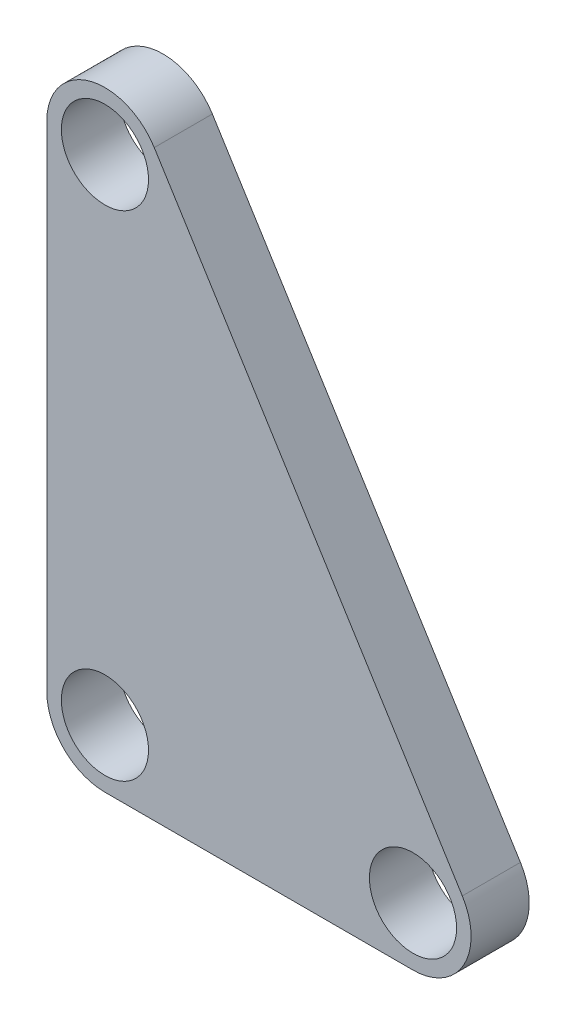
SolidWorks part; units mm, degrees
ref_plane "Front Plane" through (0, 0, 0) normal (0, 0, 1) x (1, 0, 0)
ref_plane "Top Plane" through (0, 0, 0) normal (0, 1, 0) x (1, 0, 0)
ref_plane "Right Plane" through (0, 0, 0) normal (1, 0, 0) x (0, 0, -1)
sketch "Sketch1" plane through (0, 0, 0) normal (0, 0, 1) x (1, 0, 0)
  line L0 (0, 9.5) -> (0, 1)
  line L1 (1, 0) -> (6.3, 0)
  line L2 (7.1486, 1.5291) -> (1.8486, 10.0291)
  arc A0 (1.8486, 10.0291) -> (0, 9.5) centre (1, 9.5) ccw
  arc A1 (6.3, 0) -> (7.1486, 1.5291) centre (6.3, 1) ccw
  arc A2 (0, 1) -> (1, 0) centre (1, 1) ccw
  circle A3 centre (1, 1) radius 0.75
  circle A4 centre (1, 9.5) radius 0.75
  circle A5 centre (6.3, 1) radius 0.75
  point P11 (0, 0)
  dimension "D1" = 1
  dimension "D2" = 1.5
  dimension "D3" = 1
  dimension "D4" = 1
  dimension "D7" = 1.5
  dimension "D8" = 1.5
  dimension "D5" = 8.5
  dimension "D6" = 5.3
extrude "Boss-Extrude1" add sketch "Sketch1" along normal blind 1
